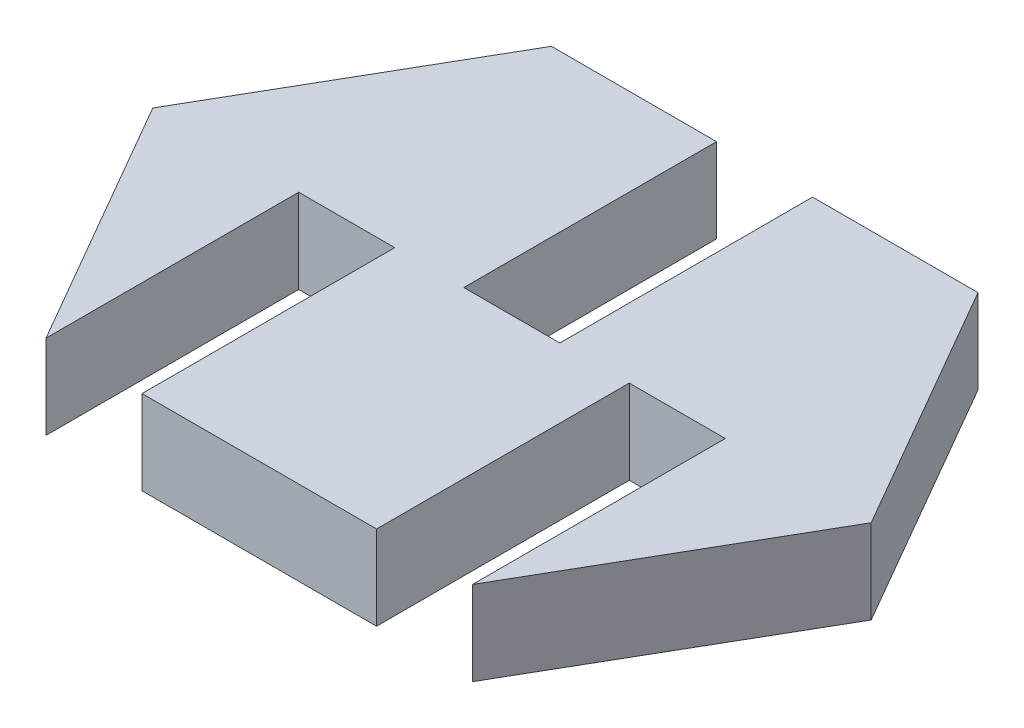
SolidWorks part; units mm, degrees
ref_plane "Front Plane" through (0, 0, 0) normal (0, 0, 1) x (1, 0, 0)
ref_plane "Top Plane" through (0, 0, 0) normal (0, 1, 0) x (1, 0, 0)
ref_plane "Right Plane" through (0, 0, 0) normal (1, 0, 0) x (0, 0, -1)
sketch "Sketch1" plane through (0, 0, 0) normal (0, 1, 0) x (1, 0, 0)
  line L0 (8.5813, -0.0094) -> (4.2512, 7.4906)
  line L7 (-8.4091, 7.4906) -> (-12.7392, -0.0094)
  line L8 (-12.7392, -0.0094) -> (-8.4091, -7.5094)
  line L9 (4.2512, -7.5094) -> (8.5813, -0.0094)
  line L10 (-8.4091, -7.5094) -> (4.2512, -7.5094)
  line L11 (4.2512, 7.4906) -> (-8.4091, 7.4906)
extrude "Boss-Extrude1" add sketch "Sketch1" along normal blind 2.5
sketch "Sketch5" plane through (0, 0, 7.5094) normal (0, 0, 1) x (1, 0, 0)
  line L0 (-8.4091, 2.5) -> (4.2512, 2.5) construction
  line L1 (-8.4091, 0) -> (-5.5591, 0)
  line L2 (-8.4091, 0) -> (-8.4091, 2.5)
  line L3 (-8.4091, 2.5) -> (-5.5591, 2.5)
  line L4 (-5.5591, 0) -> (-5.5591, 2.5)
  dimension "D1" = 2.85
extrude "Cut-Extrude2" cut sketch "Sketch5" against normal blind 7.5
sketch "Sketch6" plane through (0, 0, 7.5094) normal (0, 0, 1) x (1, 0, 0)
  line L0 (-5.5591, 2.5) -> (4.2512, 2.5) construction
  line L1 (4.2512, 0) -> (1.4012, 0)
  line L2 (4.2512, 0) -> (4.2512, 2.5)
  line L3 (4.2512, 2.5) -> (1.4012, 2.5)
  line L4 (1.4012, 0) -> (1.4012, 2.5)
  dimension "D1" = 2.85
extrude "Cut-Extrude3" cut sketch "Sketch6" against normal blind 7.5
sketch "Sketch7" plane through (0, 0, -7.4906) normal (0, 0, -1) x (-1, 0, 0)
  line L0 (-4.2512, 2.5) -> (8.4091, 2.5) construction
  line L1 (0.6588, 2.5) -> (3.5088, 2.5)
  line L2 (0.6588, 2.5) -> (0.6588, 0)
  line L3 (0.6588, 0) -> (3.5088, 0)
  line L4 (3.5088, 2.5) -> (3.5088, 0)
  line L5 (-4.2512, 0) -> (8.4091, 0) construction
  line L6 (-4.2512, 2.5) -> (-4.2512, 0) construction
  dimension "D1" = 4.91
  dimension "D2" = 2.85
extrude "Cut-Extrude4" cut sketch "Sketch7" against normal blind 7.5
